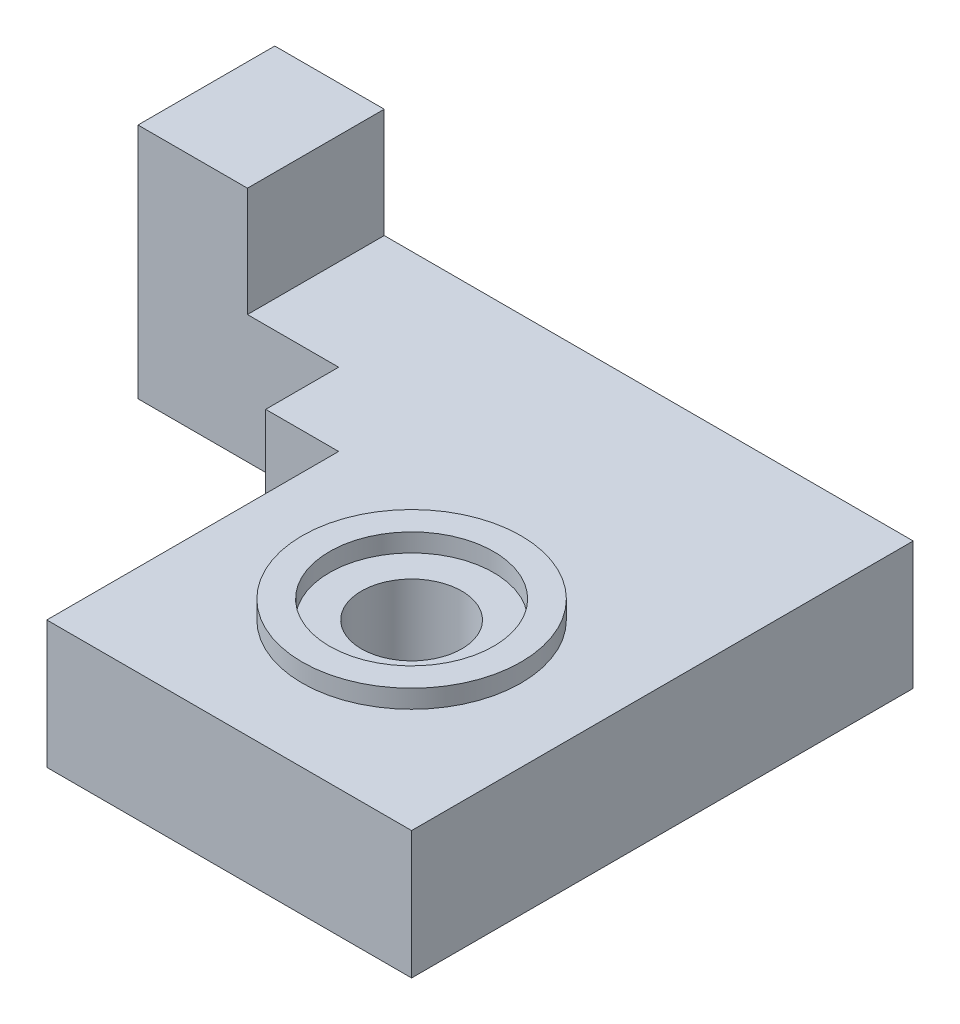
SolidWorks part; units mm, degrees
ref_plane "Front Plane" through (0, 0, 0) normal (0, 0, 1) x (1, 0, 0)
ref_plane "Top Plane" through (0, 0, 0) normal (0, 1, 0) x (1, 0, 0)
ref_plane "Right Plane" through (0, 0, 0) normal (1, 0, 0) x (0, 0, -1)
sketch "Sketch1" plane through (0, 0, 0) normal (0, 1, 0) x (1, 0, 0)
  line L1 (0, 0) -> (20, 0)
  line L2 (0, 0) -> (0, 27.5)
  line L3 (0, 27.5) -> (20, 27.5)
  line L4 (20, 0) -> (20, 27.5)
  line L5 (0, 27.5) -> (-15, 27.5)
  line L7 (0, 20) -> (-15, 20)
  line L8 (-15, 27.5) -> (-15, 20)
  dimension "D1" = 20
  dimension "D2" = 27.5
  dimension "D3" = 7.5
  dimension "D4" = 35
extrude "Boss-Extrude1" add sketch "Sketch1" along normal blind 7 contours L5 L8 L7 L2 | L1 L4 L3 L2
sketch "Sketch2" plane through (0, 7, 0) normal (0, 1, 0) x (1, 0, 0)
  line L0 (0, 20) -> (-15, 20) construction
  line L1 (-15, 27.5) -> (-9, 27.5)
  line L2 (-15, 27.5) -> (-15, 20)
  line L3 (-15, 20) -> (-9, 20)
  line L4 (-9, 27.5) -> (-9, 20)
  dimension "D1" = 6
extrude "Boss-Extrude2" add sketch "Sketch2" along normal blind 6
sketch "Sketch3" plane through (0, 7, 0) normal (0, 1, 0) x (1, 0, 0)
  line L0 (0, 0) -> (20, 20) construction
  line L1 (20, 0) -> (20, 27.5) construction
  line L2 (20, 0) -> (0, 20) construction
  point P9 (10, 10)
sketch "Sketch8" plane through (0, 7, 0) normal (0, 1, 0) x (1, 0, 0)
  circle A0 centre (10, 10) radius 6
  dimension "D1" = 12
extrude "Boss-Extrude4" add sketch "Sketch8" along normal blind 1
sketch "Sketch6" plane through (-15, 0, 0) normal (-1, 0, 0) x (0, 0, 1)
  line L0 (-25.5, 0) -> (-25.5, 13) construction
  line L1 (-27.5, 0) -> (-20, 0) construction
  line L2 (-27.5, 13) -> (-20, 13) construction
  line L3 (-27.5, 13) -> (-27.5, 0) construction
  circle A0 centre (-25.5, 9.75) radius 1
  circle A1 centre (-25.5, 3.25) radius 1
  point P8 (-25.5, 6.5)
  point P9 (-25.5, 9.75)
  point P10 (-25.5, 3.25)
  dimension "D4" = 2
  dimension "D1" = 2
  dimension "D2" = 3.25
  dimension "D3" = 3.25
extrude "Cut-Extrude1" cut sketch "Sketch6" against normal blind 4
sketch "Sketch7" plane through (0, 0, -20) normal (0, 0, 1) x (1, 0, 0)
  line L0 (0, 7) -> (-9, 7) construction
  line L1 (-4, 7) -> (0, 7)
  line L2 (-4, 7) -> (-4, -4)
  line L3 (-4, -4) -> (0, -4)
  line L4 (0, 7) -> (0, -4)
  line L5 (0, 7) -> (0, 0) construction
  dimension "D1" = 4
  dimension "D2" = 4
extrude "Boss-Extrude3" add sketch "Sketch7" along normal blind 4
hole_wizard "CBORE for M5 SBHCS2" positions "Sketch10" profile "Sketch11" counterbore size "M5" standard "ANSI Metric" end condition through all
sketch "Sketch10" plane through (0, 8, 0) normal (0, 1, 0) x (1, 0, 0)
  point P0 (10, 10)
sketch "Sketch11" plane through (10, 8, -10) normal (1, 0, 0) x (0, 0, 1)
  line L0 (0, 0) -> (0, 12)
  line L1 (0, 12) -> (2.75, 12)
  line L3 (2.75, 12) -> (2.75, 1)
  line L4 (2.75, 1) -> (4.5, 1)
  line L5 (4.5, 1) -> (4.5, 0)
  line L7 (4.5, 0) -> (0, 0)
  line L11 (0, -6.35) -> (0, 107.95) construction
  dimension "Thru Hole Dia." = 5.5
  dimension "Thru Hole Depth" = 12
  dimension "C'Bore Dia." = 9
  dimension "C'Bore Depth" = 1
chamfer "Chamfer1" distance 2 angle 45 1 edges at (-4, -4, -18)
